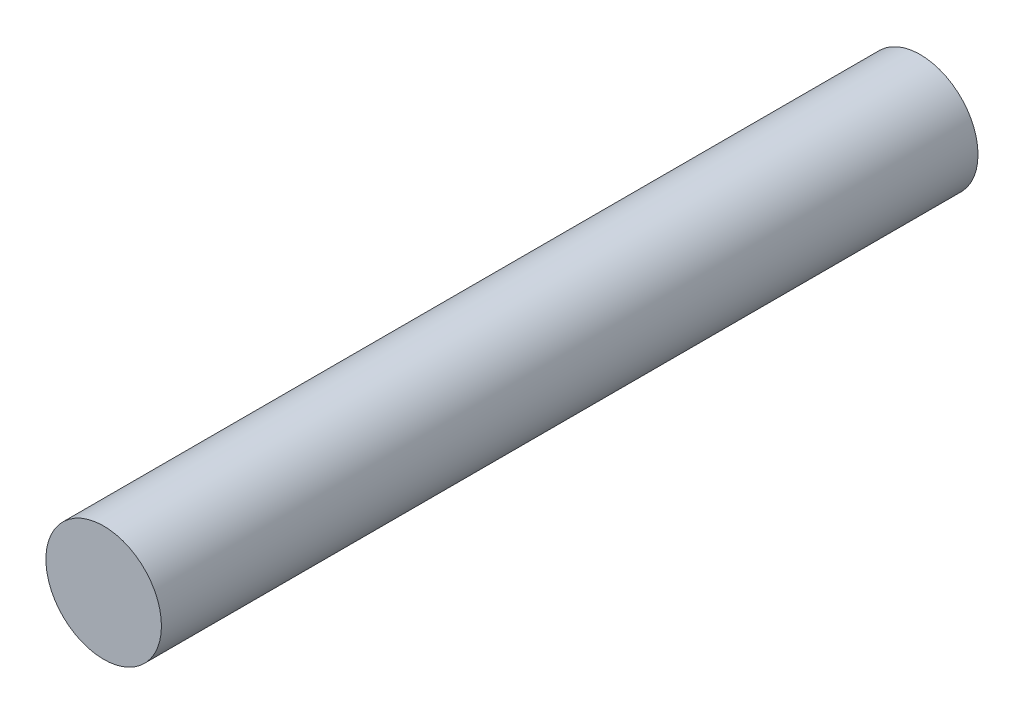
SolidWorks part; units mm, degrees
ref_plane "Alzado" through (0, 0, 0) normal (0, 0, 1) x (1, 0, 0)
ref_plane "Planta" through (0, 0, 0) normal (0, 1, 0) x (1, 0, 0)
ref_plane "Vista lateral" through (0, 0, 0) normal (1, 0, 0) x (0, 0, -1)
sketch "Croquis1" plane through (0, 0, 0) normal (0, 0, 1) x (1, 0, 0)
  circle A0 centre (0, 0) radius 7.5
  dimension "D1" = 15
extrude "Saliente-Extruir1" add sketch "Croquis1" along normal mid plane 106
